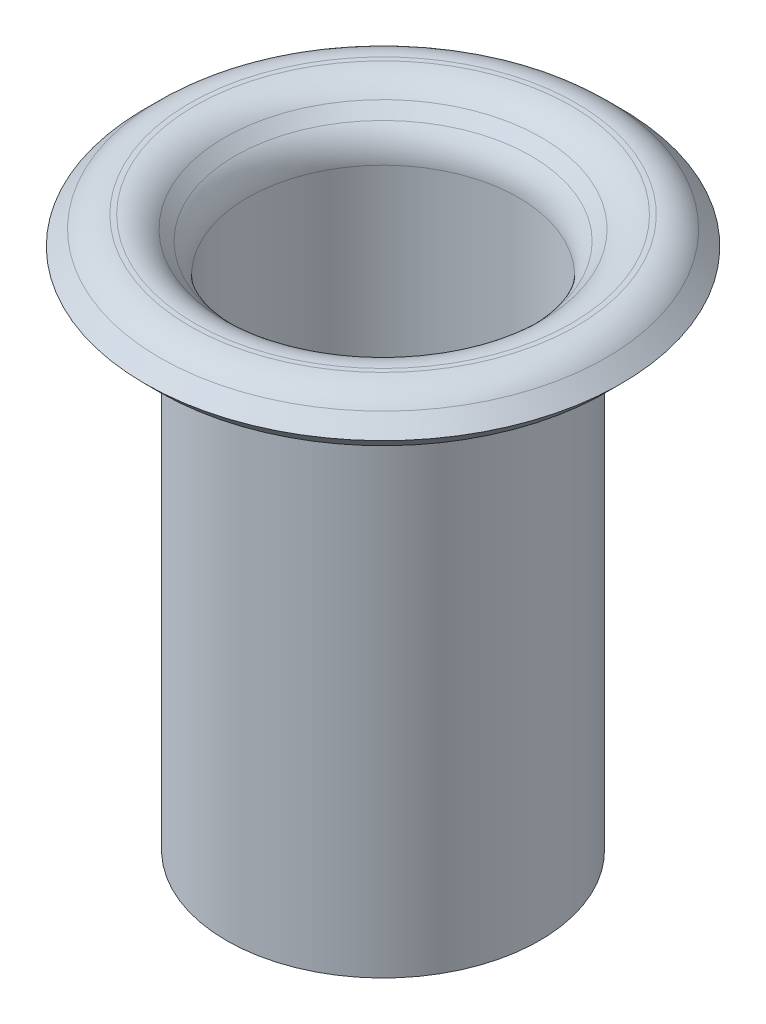
SolidWorks part; units mm, degrees
material "Laiton"
ref_plane "Plan de face" through (0, 0, 0) normal (0, 0, 1) x (1, 0, 0)
ref_plane "Plan de dessus" through (0, 0, 0) normal (0, 1, 0) x (1, 0, 0)
ref_plane "Plan de droite" through (0, 0, 0) normal (1, 0, 0) x (0, 0, -1)
sketch "Esquisse1" plane through (0, 0, 0) normal (0, 0, 1) x (1, 0, 0)
  line L0 (0, 0) -> (0, -2.6969) construction
  line L1 (-1.4972, -0.1172) -> (-1.3972, -0.2172)
  line L2 (-1.48, -0.5) -> (-1.48, -5.2)
  line L3 (-1.8257, 0) -> (-1.78, 0)
  line L4 (-1.28, -0.5) -> (-1.28, -5.2)
  line L5 (-2.25, -0.2586) -> (-2.1086, -0.4)
  line L6 (-1.28, -5.2) -> (-1.48, -5.2)
  line L7 (-2.2556, -0.2) -> (-1.6782, -0.2) construction
  line L8 (-2.1086, -0.1172) -> (-2.25, -0.2586)
  line L9 (-2.1086, -0.4) -> (-1.9672, -0.2586)
  line L10 (-2.2556, 0) -> (-1.6695, 0) construction
  line L11 (-1.8257, -0.2) -> (-1.78, -0.2)
  line L12 (-1.6386, -0.2586) -> (-1.5386, -0.3586)
  line L13 (-1.28, -0.5847) -> (-1.28, -5.2) construction
  line L14 (-1.48, -0.5474) -> (-1.48, -5.2) construction
  arc A0 (-1.9672, -0.2586) -> (-1.8257, -0.2) centre (-1.8257, -0.4) cw
  arc A1 (-1.78, -0.2) -> (-1.6386, -0.2586) centre (-1.78, -0.4) cw
  arc A2 (-1.6695, 0) -> (-1.28, -0.5847) centre (-1.7029, -0.4443) cw construction
  arc A3 (-1.6782, -0.2) -> (-1.48, -0.5474) centre (-1.7029, -0.4443) cw construction
  arc A4 (-1.5386, -0.3586) -> (-1.48, -0.5) centre (-1.68, -0.5) cw
  arc A5 (-2.1086, -0.1172) -> (-1.8257, 0) centre (-1.8257, -0.4) cw
  arc A6 (-1.78, 0) -> (-1.4972, -0.1172) centre (-1.78, -0.4) cw
  arc A7 (-1.3972, -0.2172) -> (-1.28, -0.5) centre (-1.68, -0.5) cw
  point P33 (0, 0)
  point P34 (0, 0)
  dimension "D3" = 0.2
  dimension "D7" = 45
  dimension "D1" = 4.5
  dimension "D2" = 2.96
  dimension "D5" = 5.2
  dimension "D6" = 2.56
  dimension "D8" = 45
  dimension "D9" = 0.4
  dimension "D10" = 0.5
  dimension "D11" = 4.8
  dimension "D4" = 0.2
revolve "Révolution1" add sketch "Esquisse1" angle 360 about L0
